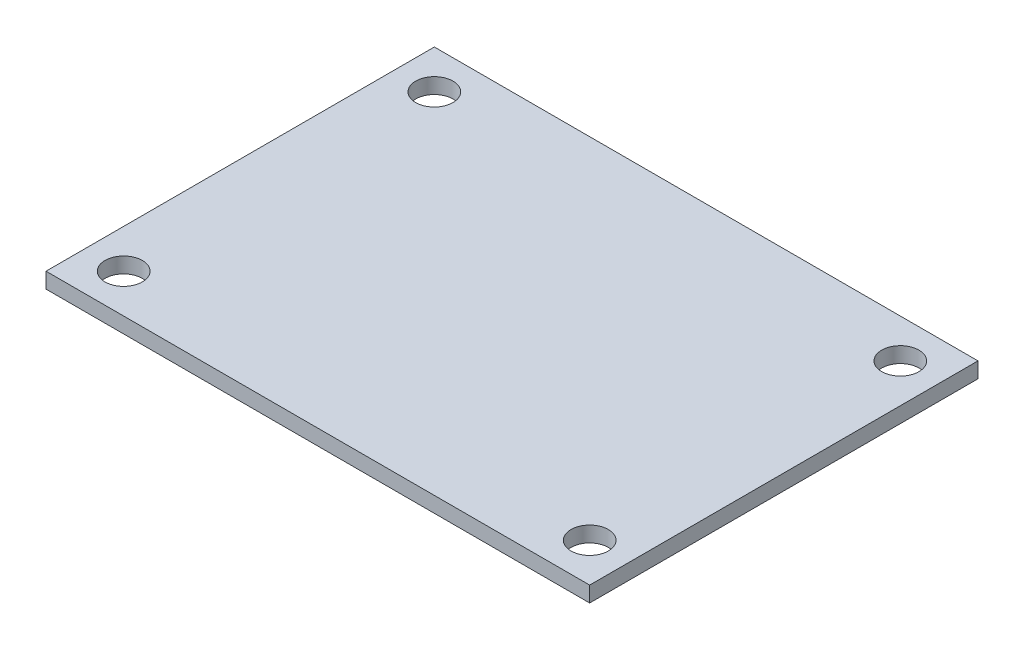
SolidWorks part; units mm, degrees
ref_plane "Přední rovina" through (0, 0, 0) normal (0, 0, 1) x (1, 0, 0)
ref_plane "Vrchní rovina" through (0, 0, 0) normal (0, 1, 0) x (1, 0, 0)
ref_plane "Pravá rovina" through (0, 0, 0) normal (1, 0, 0) x (0, 0, -1)
sketch "Skica2" plane through (0, 0, 0) normal (0, 1, 0) x (1, 0, 0)
  line L1 (-17.5, 12.5) -> (17.5, 12.5)
  line L2 (-17.5, 12.5) -> (-17.5, -12.5)
  line L3 (-17.5, -12.5) -> (17.5, -12.5)
  line L4 (17.5, 12.5) -> (17.5, -12.5)
  line L5 (-17.5, 12.5) -> (17.5, -12.5) construction
  line L6 (-17.5, -12.5) -> (17.5, 12.5) construction
  point P0 (0, 0)
  dimension "D1" = 35
  dimension "D2" = 25
extrude "Přidat vysunutím1" add sketch "Skica2" along normal blind 1
sketch "Skica3" plane through (0, 1, 0) normal (0, 1, 0) x (1, 0, 0)
  line L0 (0, 0) -> (0, 18.0543) construction
  line L1 (0, 0) -> (-22.5912, 0) construction
  circle A0 centre (-15, 10) radius 1.2
  dimension "D3" = 2.4
  dimension "D1" = 20
  dimension "D2" = 30
extrude "Odebrat vysunutím1" cut sketch "Skica3" against normal up to next (1 mm away)
pattern_linear "LinPole1" count 2 spacing 30 along (1, 0, 0) count 2 spacing 20 along (0, 0, 1) of "Odebrat vysunutím1"
